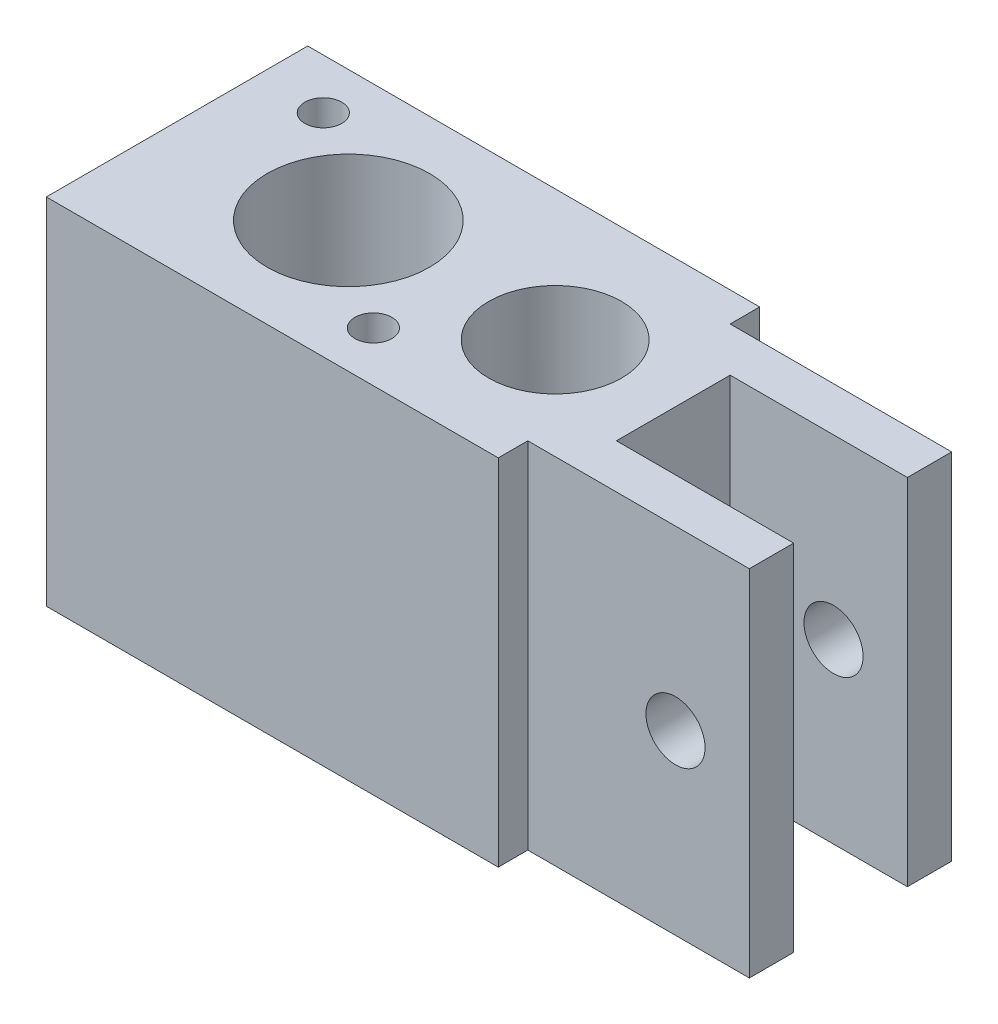
SolidWorks part; units mm, degrees
ref_plane "Ebene vorne" through (0, 0, 0) normal (0, 0, 1) x (1, 0, 0)
ref_plane "Ebene oben" through (0, 0, 0) normal (0, 1, 0) x (1, 0, 0)
ref_plane "Ebene rechts" through (0, 0, 0) normal (1, 0, 0) x (0, 0, -1)
sketch "Skizze1" plane through (0, 0, 0) normal (0, 0, 1) x (1, 0, 0)
  line L1 (-11.6, 578.1) -> (34, 578.1)
  line L2 (-11.6, 578.1) -> (-11.6, 554.1)
  line L3 (-11.6, 554.1) -> (34, 554.1)
  line L4 (34, 578.1) -> (34, 554.1)
  circle A0 centre (29, 566.1) radius 2
  point P6 (-11.6, 566.1)
sketch "Skizze2" plane through (0, 0, 0) normal (0, 1, 0) x (1, 0, 0)
  line L1 (-12.6, 8.85) -> (19, 8.85)
  line L2 (-12.6, 8.85) -> (-12.6, -8.85)
  line L3 (-12.6, 0) -> (22, 0)
  line L4 (34, 6.85) -> (34, 3.85)
  line L8 (34, 6.85) -> (19, 6.85)
  line L9 (19, 8.85) -> (19, 6.85)
  line L10 (19, -8.85) -> (19, -6.85)
  line L11 (34, -6.85) -> (19, -6.85)
  line L12 (-12.6, -8.85) -> (19, -8.85)
  line L13 (34, -3.85) -> (22, -3.85)
  line L14 (34, 3.85) -> (22, 3.85)
  line L17 (22, 3.85) -> (22, -3.85)
  line L18 (34, -3.85) -> (34, -6.85)
  circle A0 centre (14, 0) radius 4.5
  circle A1 centre (0, 0) radius 5.5
sketch "Skizze3" plane through (0, 0, 0) normal (0, 1, 0) x (1, 0, 0)
  line L0 (-12.6, -8.85) -> (-12.6, 8.85)
  line L1 (-12.6, 8.85) -> (19, 8.85)
  line L2 (19, 8.85) -> (19, 6.85)
  line L3 (19, 6.85) -> (34, 6.85)
  line L5 (-165, 0) -> (165, 0) construction
  line L6 (19, -6.85) -> (34, -6.85)
  line L7 (19, -8.85) -> (19, -6.85)
  line L8 (-12.6, -8.85) -> (19, -8.85)
  line L9 (34, 6.85) -> (34, 3.85)
  line L10 (22, -3.85) -> (22, 3.85)
  line L11 (22, 3.85) -> (34, 3.85)
  line L12 (-25.63, 0) -> (25.63, 0) construction
  line L13 (34, -6.85) -> (34, -3.85)
  line L14 (22, -3.85) -> (34, -3.85)
  circle A0 centre (0, 0) radius 5.5
  circle A1 centre (14, 0) radius 4.5
  point P21 (34, 0)
  point P24 (-12.6, 0)
  point P34 (22, 0)
sketch "Skizze5" plane through (0, 0, 0) normal (0, 0, 1) x (1, 0, 0)
  line L1 (-11.6, 578.1) -> (34, 578.1)
  line L2 (-11.6, 578.1) -> (-11.6, 554.1)
  line L3 (-11.6, 554.1) -> (34, 554.1)
  line L4 (34, 578.1) -> (34, 554.1)
  circle A0 centre (29, 566.1) radius 2
extrude "Aufsatz-Linear austragen1" add sketch "Skizze3" along normal up to vertex (578.1 mm away) up to point (34, 578.1, 0)
extrude "Schnitt-Linear austragen2" cut sketch "Skizze5" against normal through all both and the other way through all flip side to cut
sketch "Sketch2" plane through (0, 578.1, 0) normal (0, 1, 0) x (1, 0, 0)
  line L0 (-11.6, 8.85) -> (11.6, -8.85) construction
  line L1 (-12.6, -8.85) -> (19, -8.85) construction
  circle A0 centre (0, 0) radius 9
  circle A1 centre (-7.1553, 5.459) radius 1.25
  circle A2 centre (7.1553, -5.459) radius 1.25
  point P13 (-8.2363, 4.8313)
extrude "Cut-Extrude1" cut sketch "Sketch2" against normal blind 6 contours A2 | A1
